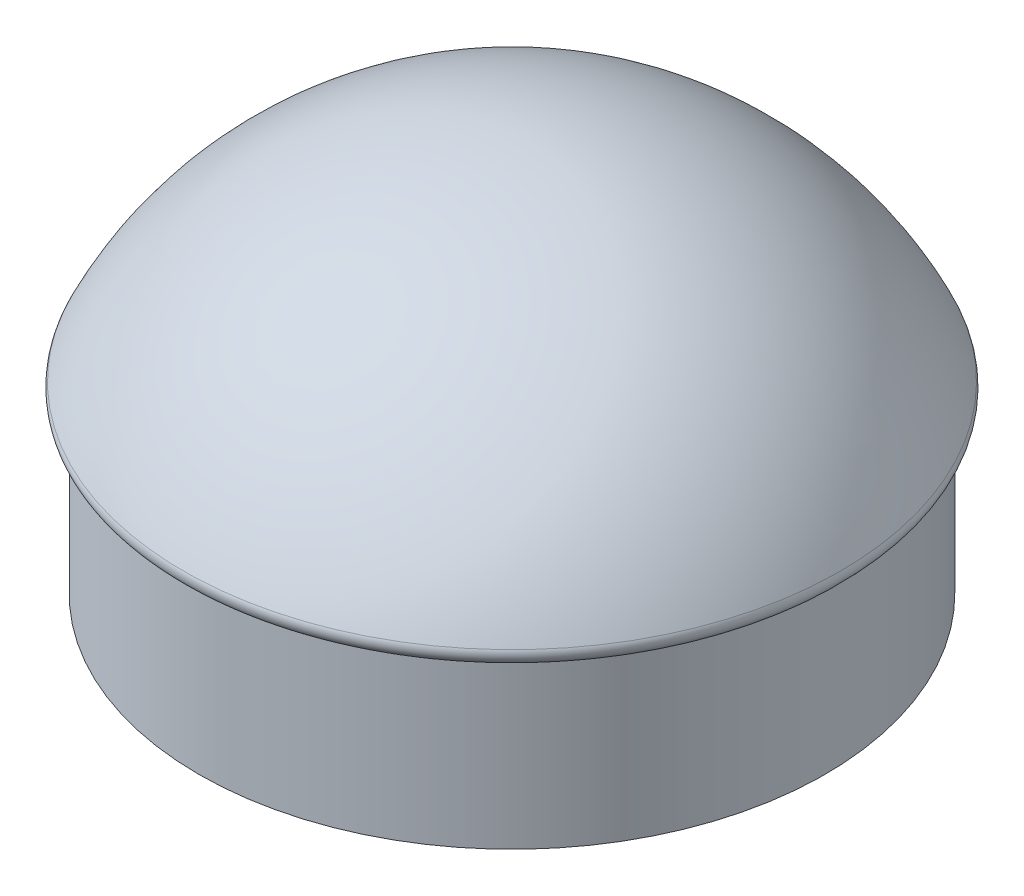
SolidWorks part; units mm, degrees
ref_plane "Front Plane" through (0, 0, 0) normal (0, 0, 1) x (1, 0, 0)
ref_plane "Top Plane" through (0, 0, 0) normal (0, 1, 0) x (1, 0, 0)
ref_plane "Right Plane" through (0, 0, 0) normal (1, 0, 0) x (0, 0, -1)
sketch "Sketch1" plane through (0, 0, 0) normal (0, 1, 0) x (1, 0, 0)
  circle A0 centre (0, 0) radius 140
  dimension "D1" = 280
extrude "Boss-Extrude1" add sketch "Sketch1" along normal blind 75
sketch "Sketch3" plane through (0, 0, 0) normal (1, 0, 0) x (0, 0, -1)
  line L0 (0, 75) -> (0, 175)
  line L1 (140, 75) -> (-140, 75) construction
  line L2 (0, 0) -> (0, 150)
  line L3 (0, 75) -> (142.3273, 75)
  line L4 (150, 75) -> (-150, 75)
  arc A0 (0, 175) -> (146.851, 82.1297) centre (0.4816, 13.2224) cw
  arc A1 (142.3273, 75) -> (146.851, 82.1297) centre (142.3273, 80) ccw
  point P12 (-32.0544, 75)
  dimension "D2" = 300
  dimension "D3" = 5
  dimension "D1" = 150
revolve "Revolve1" add sketch "Sketch3" angle 360 about L2
